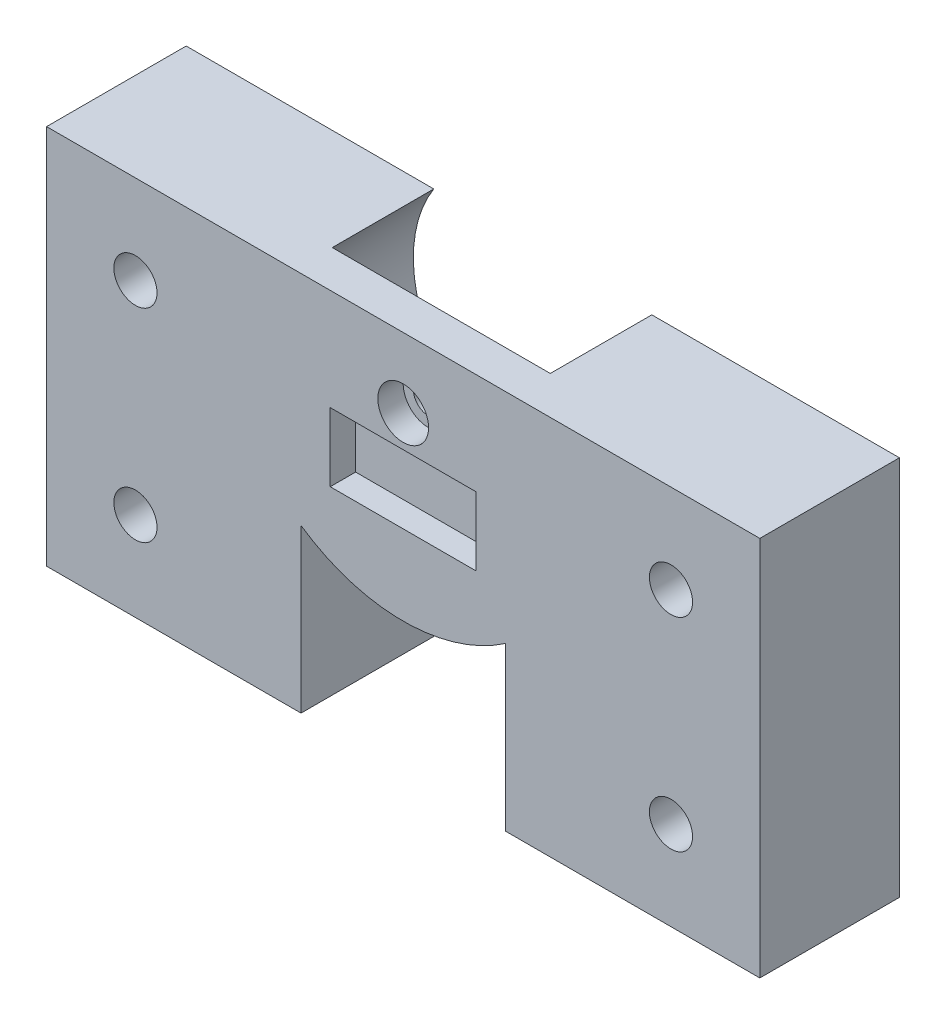
SolidWorks part; units mm, degrees
ref_plane "Front Plane" through (0, 0, 0) normal (0, 0, 1) x (1, 0, 0)
ref_plane "Top Plane" through (0, 0, 0) normal (0, 1, 0) x (1, 0, 0)
ref_plane "Right Plane" through (0, 0, 0) normal (1, 0, 0) x (0, 0, -1)
sketch "Sketch1" plane through (0, 0, 0) normal (0, 0, 1) x (1, 0, 0)
  line L0 (19.5099, 0) -> (0, 0)
  line L1 (28.1, -5.5) -> (28.1, -10) construction
  line L2 (0, 0) -> (0, -30)
  line L3 (0, -30) -> (56.2, -30)
  line L4 (36.6901, 0) -> (56.2, 0)
  line L5 (56.2, 0) -> (56.2, -30)
  line L6 (19.5099, 0) -> (36.6901, 0) construction
  line L7 (35.8259, 0) -> (36.6901, 0)
  line L8 (35.8259, -3) -> (37.9889, -3)
  line L18 (0, -15) -> (56.2, -15) construction
  arc A0 (19.5099, 0) -> (37.9889, -3) centre (28.1, -5.5) ccw
  arc A1 (35.8259, 0) -> (35.8259, -3) centre (35.8259, -1.5) ccw
  dimension "D4" = 30
  dimension "D5" = 1.5
  dimension "D2" = 5.5
  dimension "D1" = 10.2
  dimension "D3" = 56.2
extrude "Boss-Extrude1" add sketch "Sketch1" along normal blind 8
sketch "Sketch2" [suppressed] plane through (0, 0, 0) normal (0, 0, -1) x (-1, 0, 0)
  line L0 (-56.2, -15) -> (0, -15) construction
  line L1 (-56.2, -30) -> (-56.2, 0) construction
  line L2 (-46.0015, -7) -> (-47.6007, -4.23)
  line L3 (-47.6007, -4.23) -> (-50.7993, -4.23)
  line L4 (-50.7993, -4.23) -> (-52.3985, -7)
  line L5 (-52.3985, -7) -> (-50.7993, -9.77)
  line L6 (-50.7993, -9.77) -> (-47.6007, -9.77)
  line L7 (-47.6007, -9.77) -> (-46.0015, -7)
  line L8 (0, 0) -> (0, -30) construction
  line L9 (-8.5993, -9.77) -> (-10.1985, -7)
  line L10 (-28.1, 0) -> (-28.1, -30) construction
  line L11 (0, -30) -> (-56.2, -30) construction
  line L12 (-5.4007, -9.77) -> (-8.5993, -9.77)
  line L13 (-3.8015, -7) -> (-5.4007, -9.77)
  line L14 (-5.4007, -4.23) -> (-3.8015, -7)
  line L15 (-8.5993, -4.23) -> (-5.4007, -4.23)
  line L16 (-10.1985, -7) -> (-8.5993, -4.23)
  line L17 (-10.1985, -23) -> (-8.5993, -25.77)
  line L18 (-8.5993, -25.77) -> (-5.4007, -25.77)
  line L19 (-5.4007, -25.77) -> (-3.8015, -23)
  line L20 (-3.8015, -23) -> (-5.4007, -20.23)
  line L21 (-5.4007, -20.23) -> (-8.5993, -20.23)
  line L22 (-8.5993, -20.23) -> (-10.1985, -23)
  line L23 (-47.6007, -20.23) -> (-46.0015, -23)
  line L24 (-50.7993, -20.23) -> (-47.6007, -20.23)
  line L25 (-52.3985, -23) -> (-50.7993, -20.23)
  line L26 (-50.7993, -25.77) -> (-52.3985, -23)
  line L27 (-47.6007, -25.77) -> (-50.7993, -25.77)
  line L28 (-46.0015, -23) -> (-47.6007, -25.77)
  circle A0 centre (-49.2, -7) radius 2.77 construction
  circle A1 centre (-7, -7) radius 2.77 construction
  circle A2 centre (-7, -23) radius 2.77 construction
  circle A3 centre (-49.2, -23) radius 2.77 construction
  dimension "D1" = 5.54
  dimension "D2" = 7
  dimension "D3" = 7
extrude "Cut-Extrude1" [suppressed] cut sketch "Sketch2" against normal blind 2.4
sketch "Sketch3" plane through (0, 0, 8) normal (0, 0, 1) x (1, 0, 0)
  line L0 (0, 0) -> (0, -30)
  line L1 (0, -30) -> (56.2, -30)
  line L2 (56.2, -30) -> (56.2, 0) construction
  line L3 (56.2, -30) -> (56.2, 0)
  line L4 (0, 0) -> (56.2, 0)
extrude "Boss-Extrude2" add sketch "Sketch3" along normal blind 3
sketch "Sketch4" plane through (0, 0, 0) normal (0, 0, -1) x (-1, 0, 0)
  line L0 (-56.2, -15) -> (0, -15) construction
  line L1 (-56.2, -30) -> (-56.2, 0) construction
  line L2 (0, 0) -> (0, -30) construction
  line L3 (-28.1, -5.5) -> (-28.1, -30) construction
  line L8 (0, -30) -> (-56.2, -30) construction
  circle A0 centre (-49.2, -7) radius 1.7
  circle A1 centre (-7, -7) radius 1.7
  circle A2 centre (-7, -23) radius 1.7
  circle A3 centre (-49.2, -23) radius 1.7
  circle A4 centre (-28.1, -5.5) radius 1.2
  arc A5 (-37.9889, -3) -> (-19.5099, 0) centre (-28.1, -5.5) ccw construction
  dimension "D1" = 3.4
  dimension "D4" = 2.4
  dimension "D2" = 7
  dimension "D3" = 7
extrude "Cut-Extrude2" cut sketch "Sketch4" against normal up to surface (11 mm away) up to face at (28.1, -15, 11)
sketch "Sketch5" plane through (0, 0, 0) normal (0, 0, -1) x (-1, 0, 0)
  line L0 (-19.5099, 0) -> (-36.6901, 0)
  line L1 (-56.2, 0) -> (-35.8259, 0) construction
  arc A0 (-36.6901, 0) -> (-19.5099, 0) centre (-28.1, -5.5) ccw
extrude "Cut-Extrude3" cut sketch "Sketch5" against normal up to surface (8 mm away) up to face at (29.3, -5.5, 8)
sketch "Sketch7" plane through (0, 0, 11) normal (0, 0, 1) x (1, 0, 0)
  line L0 (28.1, -5.5) -> (28.1, -30) construction
  line L1 (22.35, -8) -> (33.85, -8)
  line L2 (22.35, -8) -> (22.35, -13.4)
  line L3 (22.35, -13.4) -> (33.85, -13.4)
  line L4 (33.85, -8) -> (33.85, -13.4)
  line L5 (0, -30) -> (56.2, -30) construction
  circle A0 centre (28.1, -5.5) radius 2
  dimension "D1" = 4
  dimension "D2" = 5.75
  dimension "D3" = 5.4
  dimension "D4" = 8
  dimension "D5" = 5.75
extrude "Cut-Extrude4" cut sketch "Sketch7" against normal blind 2
sketch "Sketch8" plane through (0, 0, 11) normal (0, 0, 1) x (1, 0, 0)
  line L0 (28.1, 0) -> (28.1, -30) construction
  line L1 (56.2, 0) -> (0, 0) construction
  line L2 (0, -30) -> (56.2, -30) construction
  line L3 (0, -15) -> (56.2, -15) construction
  line L4 (0, 0) -> (0, -30) construction
  line L5 (56.2, -30) -> (56.2, 0) construction
  circle A0 centre (7, -7) radius 2.875
  circle A1 centre (49.2, -7) radius 2.875
  circle A2 centre (49.2, -23) radius 2.875
  circle A3 centre (7, -23) radius 2.875
  dimension "D1" = 5.75
extrude "Cut-Extrude5" [suppressed] cut sketch "Sketch8" against normal blind 3
sketch "Sketch9" plane through (0, 0, 0) normal (0, 0, 1) x (1, 0, 0)
  line L0 (23, -30) -> (33.2, -30) construction
  line L1 (0, -30) -> (56.2, -30) construction
  line L2 (33.2, -30) -> (36.15, -30) construction
  line L3 (28.1, -5.5) -> (28.1, -30) construction
  line L4 (36.15, -30) -> (36.15, -17.1978)
  line L5 (36.15, -30) -> (20.05, -30)
  line L6 (23, -30) -> (20.05, -30) construction
  line L7 (20.05, -30) -> (20.05, -17.1978)
  circle A0 centre (28.1, -5.5) radius 14.2 construction
  circle A3 centre (28.1, -5.5) radius 10.2 construction
  arc A4 (20.05, -17.1978) -> (36.15, -17.1978) centre (28.1, -5.5) ccw
  dimension "D1" = 28.4
  dimension "D2" = 20.4
  dimension "D3" = 5.1
  dimension "D4" = 2.95
extrude "Cut-Extrude6" cut sketch "Sketch9" along normal up to next
